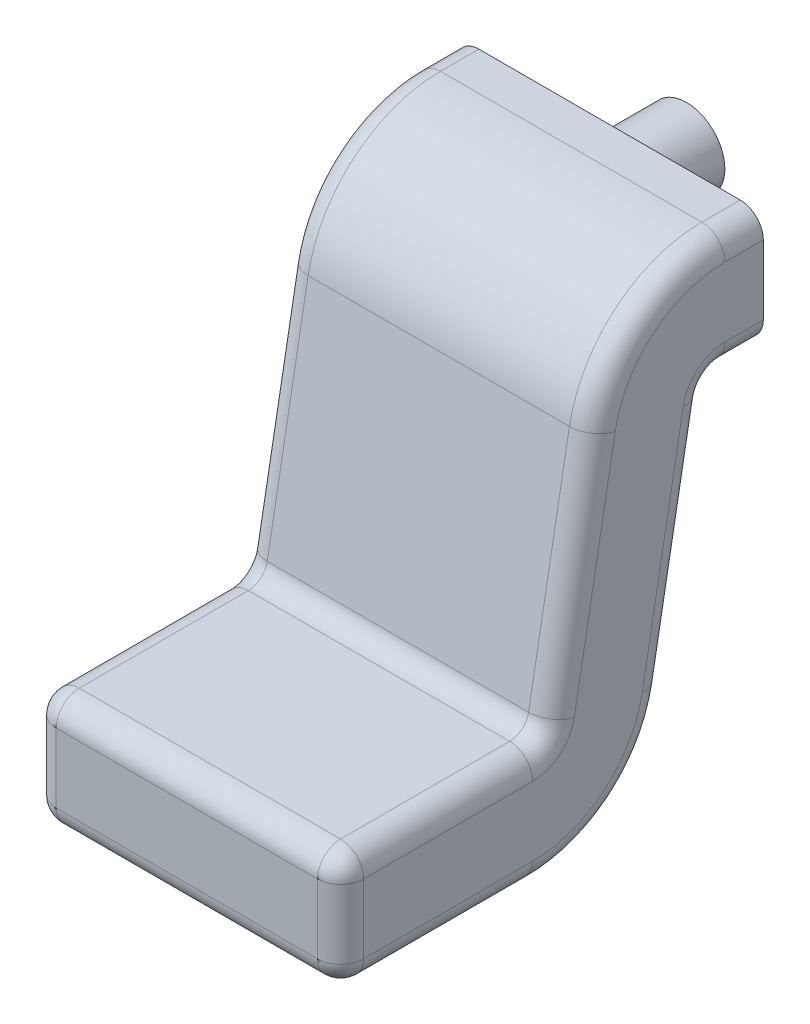
SolidWorks part; units mm, degrees
material "Aço inoxidável fundido"
ref_plane "Plano frontal" through (0, 0, 0) normal (0, 0, 1) x (1, 0, 0)
ref_plane "Plano superior" through (0, 0, 0) normal (0, 1, 0) x (1, 0, 0)
ref_plane "Plano direito" through (0, 0, 0) normal (1, 0, 0) x (0, 0, -1)
sketch "Esboço1" plane through (0, 0, 0) normal (0, 0, 1) x (1, 0, 0)
  line L1 (-0.17, -0.075) -> (0.17, -0.075)
  line L2 (-0.2, -0.045) -> (-0.2, 0.045)
  line L3 (-0.17, 0.075) -> (0.17, 0.075)
  line L4 (0.2, -0.045) -> (0.2, 0.045)
  line L5 (-0.2, -0.075) -> (0.2, 0.075) construction
  line L6 (-0.2, 0.075) -> (0.2, -0.075) construction
  arc A0 (-0.17, 0.075) -> (-0.2, 0.045) centre (-0.17, 0.045) ccw
  arc A1 (-0.2, -0.045) -> (-0.17, -0.075) centre (-0.17, -0.045) ccw
  arc A2 (0.17, -0.075) -> (0.2, -0.045) centre (0.17, -0.045) ccw
  arc A3 (0.17, 0.075) -> (0.2, 0.045) centre (0.17, 0.045) cw
  point P0 (0, 0)
  dimension "D3" = 0.03
  dimension "D1" = 0.4
  dimension "D2" = 0.15
sketch "Esboço2" plane through (0, 0, 0) normal (1, 0, 0) x (0, 0, -1)
  line L0 (0, 0) -> (0.25, 0)
  line L1 (0.3484, 0.0823) -> (0.4016, 0.3777)
  line L2 (0.5, 0.46) -> (0.55, 0.46)
  arc A0 (0.25, 0) -> (0.3484, 0.0823) centre (0.25, 0.1) ccw
  arc A1 (0.5, 0.46) -> (0.4016, 0.3777) centre (0.5, 0.36) ccw
  point P7 (0.3336, 0)
  point P10 (0.4164, 0.46)
  dimension "D5" = 0.1
  dimension "D1" = 0.25
  dimension "D2" = 0.25
  dimension "D3" = 0.05
  dimension "D4" = 0.46
sweep "Varredura1" add profiles "Esboço1" path "Esboço2"
fillet "Filete2" radius 0.03 8 edges at (0, 0.075, 0) (0.1912, 0.0662, 0) (0.2, 0, 0) (0.1912, -0.0662, 0) (0, -0.075, 0) (-0.1912, -0.0662, 0) (-0.2, 0, 0) (-0.1912, 0.0662, 0)
sketch "Esboço3" plane through (0, 0, -0.55) normal (0, 0, -1) x (-1, 0, 0)
  line L0 (0, 0.785) -> (0, 0.635) construction
  line L5 (0.2, 0.505) -> (0.2, 0.415) construction
  line L6 (-0.2, 0.415) -> (-0.2, 0.505) construction
  line L7 (-0.2, 0.46) -> (0.2, 0.46) construction
  line L8 (-0.17, 0.535) -> (0.17, 0.535) construction
  line L9 (0.17, 0.385) -> (-0.17, 0.385) construction
  circle A0 centre (0, 0.46) radius 0.05
  dimension "D1" = 0.1
extrude "Ressalto-extrusão1" add sketch "Esboço3" along normal blind 0.1
